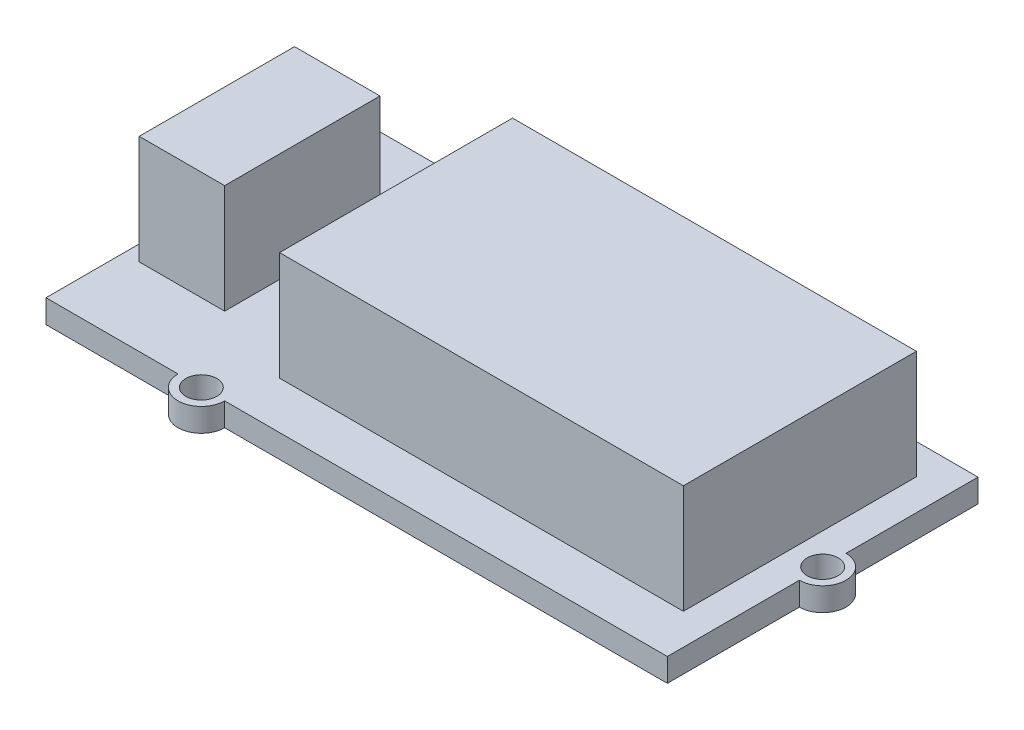
SolidWorks part; units mm, degrees
ref_plane "Front Plane" through (0, 0, 0) normal (0, 0, 1) x (1, 0, 0)
ref_plane "Top Plane" through (0, 0, 0) normal (0, 1, 0) x (1, 0, 0)
ref_plane "Right Plane" through (0, 0, 0) normal (1, 0, 0) x (0, 0, -1)
sketch "Sketch1" plane through (0, 0, 0) normal (0, 1, 0) x (1, 0, 0)
  line L1 (-20, 10) -> (20, 10)
  line L2 (-20, 10) -> (-20, -10)
  line L3 (-20, -10) -> (20, -10)
  line L4 (20, 10) -> (20, -10)
  line L5 (-20, 10) -> (20, -10) construction
  line L6 (-20, -10) -> (20, 10) construction
  point P0 (0, 0)
  dimension "D1" = 20
  dimension "D2" = 40
extrude "Boss-Extrude1" add sketch "Sketch1" along normal blind 1.5
sketch "Sketch2" plane through (0, 1.5, 0) normal (0, 1, 0) x (1, 0, 0)
  line L0 (20, 10) -> (-20, 10) construction
  line L1 (-20, -10) -> (20, -10) construction
  line L2 (20, -10) -> (20, 10) construction
  line L3 (-20, 10) -> (-20, -10) construction
  circle A0 centre (-10, 10) radius 1.5
  circle A1 centre (-10, -10) radius 1.5
  circle A2 centre (20, 0) radius 1.5
  dimension "D1" = 3
  dimension "D2" = 3
  dimension "D3" = 3
  dimension "D4" = 10
  dimension "D5" = 10
  dimension "D6" = 10
extrude "Boss-Extrude3" add sketch "Sketch2" against normal blind 1.5
sketch "Sketch3" plane through (0, 1.5, 0) normal (0, 1, 0) x (1, 0, 0)
  circle A0 centre (-10, -10) radius 1
  circle A1 centre (20, 0) radius 1
  circle A2 centre (-10, 10) radius 1
  dimension "D1" = 2
  dimension "D2" = 2
  dimension "D3" = 2
extrude "Cut-Extrude1" cut sketch "Sketch3" against normal blind 1.5
sketch "Sketch4" plane through (0, 1.5, 0) normal (0, 1, 0) x (1, 0, 0)
  line L1 (-19, 5) -> (-13.5, 5)
  line L2 (-19, 5) -> (-19, -5)
  line L3 (-19, -5) -> (-13.5, -5)
  line L4 (-13.5, 5) -> (-13.5, -5)
  line L5 (-19, 5) -> (-13.5, -5) construction
  line L6 (-19, -5) -> (-13.5, 5) construction
  line L7 (-20, -10) -> (-11.5, -10) construction
  line L9 (-20, 10) -> (-20, -10) construction
  point P0 (-16.25, 0)
  dimension "D1" = 5.5
  dimension "D2" = 10
  dimension "D3" = 5
  dimension "D4" = 1
extrude "Boss-Extrude4" add sketch "Sketch4" along normal blind 7
sketch "Sketch5" plane through (0, 1.5, 0) normal (0, 1, 0) x (1, 0, 0)
  line L0 (-20, 10) -> (-20, -10) construction
  line L1 (-8, 8.0339) -> (18, 8.0339)
  line L2 (-8, 8.0339) -> (-8, -6.9661)
  line L3 (-8, -6.9661) -> (18, -6.9661)
  line L4 (18, 8.0339) -> (18, -6.9661)
  line L5 (-8, 8.0339) -> (18, -6.9661) construction
  line L6 (-8, -6.9661) -> (18, 8.0339) construction
  point P0 (5, 0.5339)
  dimension "D1" = 15
  dimension "D2" = 26
  dimension "D3" = 12
extrude "Boss-Extrude5" add sketch "Sketch5" along normal blind 7
